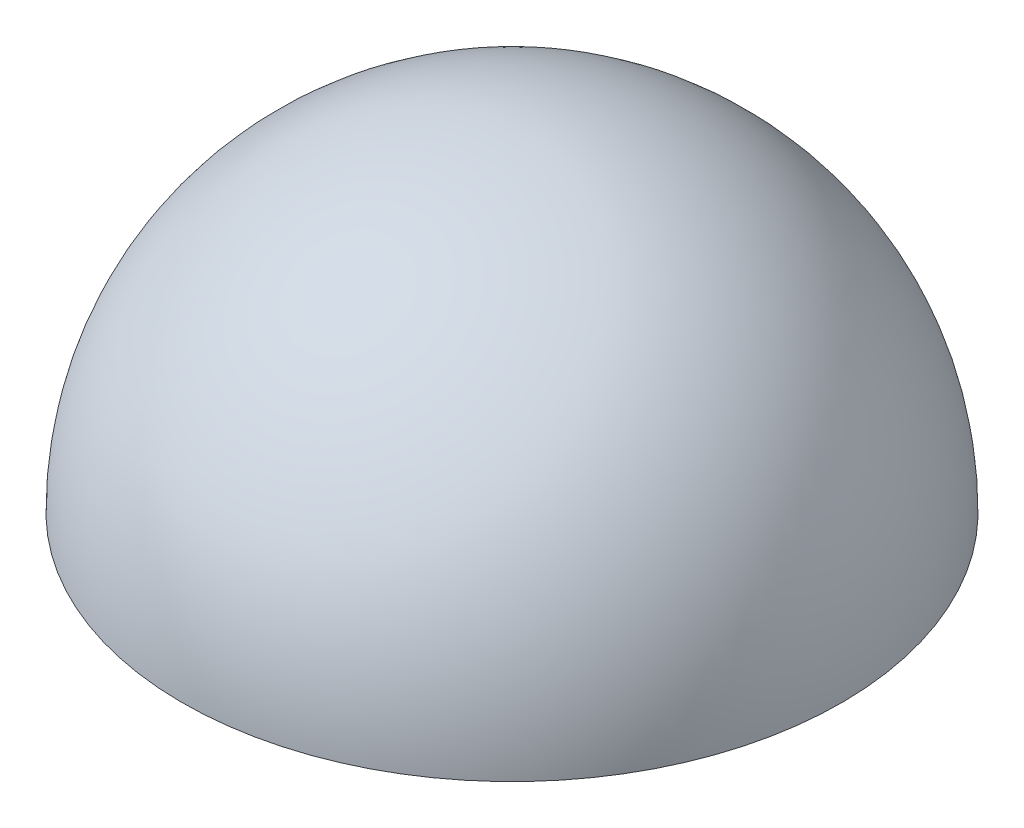
SolidWorks part; units mm, degrees
ref_plane "Front Plane" through (0, 0, 0) normal (0, 0, 1) x (1, 0, 0)
ref_plane "Top Plane" through (0, 0, 0) normal (0, 1, 0) x (1, 0, 0)
ref_plane "Right Plane" through (0, 0, 0) normal (1, 0, 0) x (0, 0, -1)
sketch "Sketch1" plane through (0, 0, 0) normal (0, 1, 0) x (1, 0, 0)
  line L0 (-33.5889, 83.619) -> (-24.0764, -62.1209)
  circle A0 centre (-28.8326, 10.749) radius 73.025
  dimension "D1" = 146.05
revolve "Revolve1" add sketch "Sketch1" angle 180 about L0
